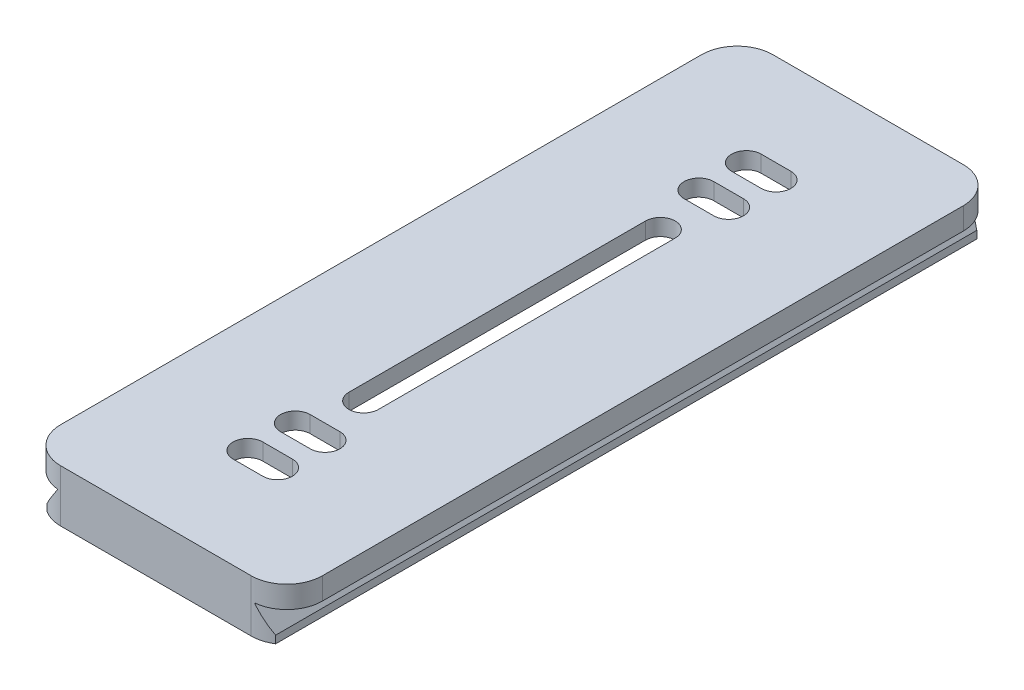
SolidWorks part; units mm, degrees
ref_plane "Front Plane" through (0, 0, 0) normal (0, 0, 1) x (1, 0, 0)
ref_plane "Top Plane" through (0, 0, 0) normal (0, 1, 0) x (1, 0, 0)
ref_plane "Right Plane" through (0, 0, 0) normal (1, 0, 0) x (0, 0, -1)
sketch "Sketch1" plane through (0, 0, 0) normal (0, 1, 0) x (1, 0, 0)
  line L0 (0, -25) -> (0, 25) construction
  line L1 (-22.05, -60) -> (22.05, -60)
  line L2 (-22.05, -60) -> (-22.05, 60)
  line L3 (-22.05, 60) -> (22.05, 60)
  line L4 (22.05, -60) -> (22.05, 60)
  line L5 (-22.05, -60) -> (22.05, 60) construction
  line L6 (-22.05, 60) -> (22.05, -60) construction
  line L7 (-2.5, -25) -> (-2.5, 25)
  line L8 (2.5, -25) -> (2.5, 25)
  line L9 (0, 0) -> (22.05, 0) construction
  line L10 (0, 25) -> (0, 60) construction
  line L11 (-2.5, 34) -> (2.5, 34) construction
  line L12 (-2.5, 36.5) -> (2.5, 36.5)
  line L13 (-2.5, 31.5) -> (2.5, 31.5)
  line L14 (-2.5, 42) -> (2.5, 42) construction
  line L15 (-2.5, 44.5) -> (2.5, 44.5)
  line L16 (-2.5, 39.5) -> (2.5, 39.5)
  line L17 (-2.5, -42) -> (2.5, -42) construction
  line L18 (-2.5, -44.5) -> (2.5, -44.5)
  line L19 (-2.5, -39.5) -> (2.5, -39.5)
  line L20 (-2.5, -34) -> (2.5, -34) construction
  line L21 (-2.5, -36.5) -> (2.5, -36.5)
  line L22 (-2.5, -31.5) -> (2.5, -31.5)
  arc A0 (-2.5, -25) -> (2.5, -25) centre (0, -25) ccw
  arc A1 (2.5, 25) -> (-2.5, 25) centre (0, 25) ccw
  arc A2 (-2.5, 36.5) -> (-2.5, 31.5) centre (-2.5, 34) ccw
  arc A3 (2.5, 31.5) -> (2.5, 36.5) centre (2.5, 34) ccw
  arc A4 (-2.5, 44.5) -> (-2.5, 39.5) centre (-2.5, 42) ccw
  arc A5 (2.5, 39.5) -> (2.5, 44.5) centre (2.5, 42) ccw
  arc A6 (-2.5, -44.5) -> (-2.5, -39.5) centre (-2.5, -42) cw
  arc A7 (2.5, -39.5) -> (2.5, -44.5) centre (2.5, -42) cw
  arc A8 (-2.5, -36.5) -> (-2.5, -31.5) centre (-2.5, -34) cw
  arc A9 (2.5, -31.5) -> (2.5, -36.5) centre (2.5, -34) cw
  point P0 (0, 0)
  point P8 (0, 0)
  point P19 (0, 34)
  point P26 (0, 42)
  point P33 (0, -42)
  point P40 (0, -34)
  dimension "D6" = 2.5
  dimension "D8" = 42
  dimension "D1" = 44.1
  dimension "D2" = 120
  dimension "D3" = 50
  dimension "D4" = 5
  dimension "D5" = 34
  dimension "D7" = 5
extrude "Boss-Extrude1" add sketch "Sketch1" along normal blind 8.8
fillet "Fillet1" radius 6 4 edges at (-22.05, 4.4, 60) (-22.05, 4.4, -60) (22.05, 4.4, -60) (22.05, 4.4, 60)
sketch "Sketch2" plane through (0, 0, 60) normal (0, 0, 1) x (1, 0, 0)
  line L0 (19.25, 0) -> (19.25, 1.2703)
  line L2 (16.05, 0) -> (22.05, 0) construction
  line L3 (19.25, 1.2703) -> (16.65, 4.9584)
  line L4 (16.65, 4.9584) -> (16.65, 5.1)
  line L5 (16.65, 5.1) -> (22.05, 5.1)
  line L6 (22.05, 8.8) -> (22.05, 0) construction
  line L7 (22.05, 5.1) -> (22.05, 0)
  line L8 (22.05, 0) -> (19.25, 0)
  line L9 (0, 0) -> (0, 8.8) construction
  line L10 (-16.05, 8.8) -> (16.05, 8.8) construction
  line L11 (22.05, 8.8) -> (16.05, 8.8) construction
  line L12 (-22.05, 0) -> (-19.25, 0)
  line L13 (-22.05, 5.1) -> (-22.05, 0)
  line L14 (-16.65, 5.1) -> (-22.05, 5.1)
  line L15 (-16.65, 4.9584) -> (-16.65, 5.1)
  line L16 (-19.25, 1.2703) -> (-16.65, 4.9584)
  line L17 (-19.25, 0) -> (-19.25, 1.2703)
  dimension "D1" = 38.5
  dimension "D2" = 33.3
  dimension "D3" = 3.7
extrude "Cut-Extrude1" cut sketch "Sketch2" against normal through all
sketch "Sketch3" plane through (0, 0, 0) normal (0, -1, 0) x (1, 0, 0)
  line L0 (19.25, -59.0754) -> (19.25, 59.0754) construction
  line L1 (-8.95, -55) -> (8.95, -55)
  line L2 (-13.95, -50) -> (-13.95, 50)
  line L3 (-8.95, 55) -> (8.95, 55)
  line L4 (13.95, -50) -> (13.95, 50)
  line L5 (-13.95, -55) -> (13.95, 55) construction
  line L6 (-13.95, 55) -> (13.95, -55) construction
  line L7 (-16.05, 60) -> (16.05, 60) construction
  arc A0 (-13.95, -50) -> (-8.95, -55) centre (-8.95, -50) ccw
  arc A1 (8.95, -55) -> (13.95, -50) centre (8.95, -50) ccw
  arc A2 (-13.95, 50) -> (-8.95, 55) centre (-8.95, 50) cw
  arc A3 (13.95, 50) -> (8.95, 55) centre (8.95, 50) ccw
  point P0 (0, 0)
  dimension "D3" = 5
  dimension "D1" = 5.3
  dimension "D2" = 5
extrude "Cut-Extrude2" cut sketch "Sketch3" against normal blind 6
